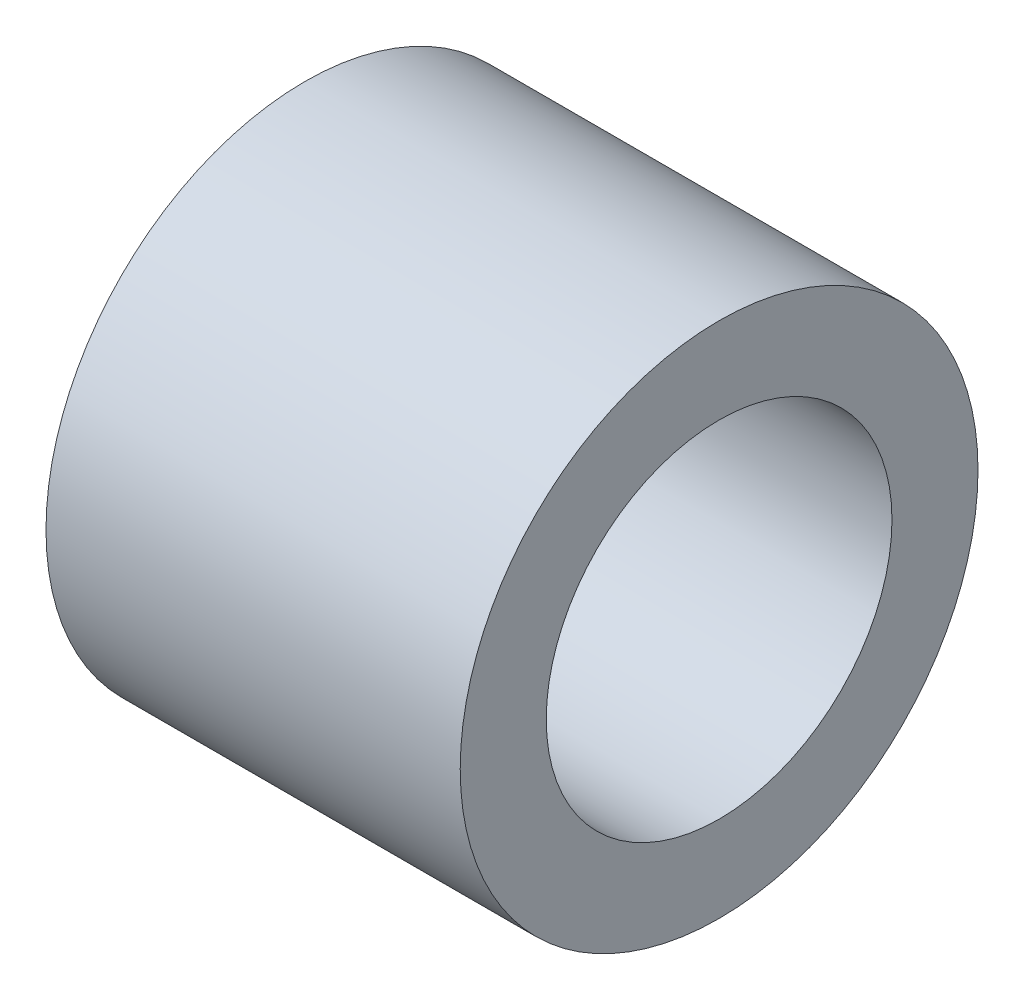
SolidWorks part; units mm, degrees
ref_plane "Front Plane" through (0, 0, 0) normal (0, 0, 1) x (1, 0, 0)
ref_plane "Top Plane" through (0, 0, 0) normal (0, 1, 0) x (1, 0, 0)
ref_plane "Right Plane" through (0, 0, 0) normal (1, 0, 0) x (0, 0, -1)
sketch "Sketch1" plane through (0, 0, 0) normal (1, 0, 0) x (0, 0, -1)
  circle A0 centre (0, 0) radius 2.65
  circle A1 centre (0, 0) radius 3.9688
  dimension "D1" = 5.3
  dimension "D2" = 7.9375
extrude "Boss-Extrude1" add sketch "Sketch1" along normal blind 6.35
